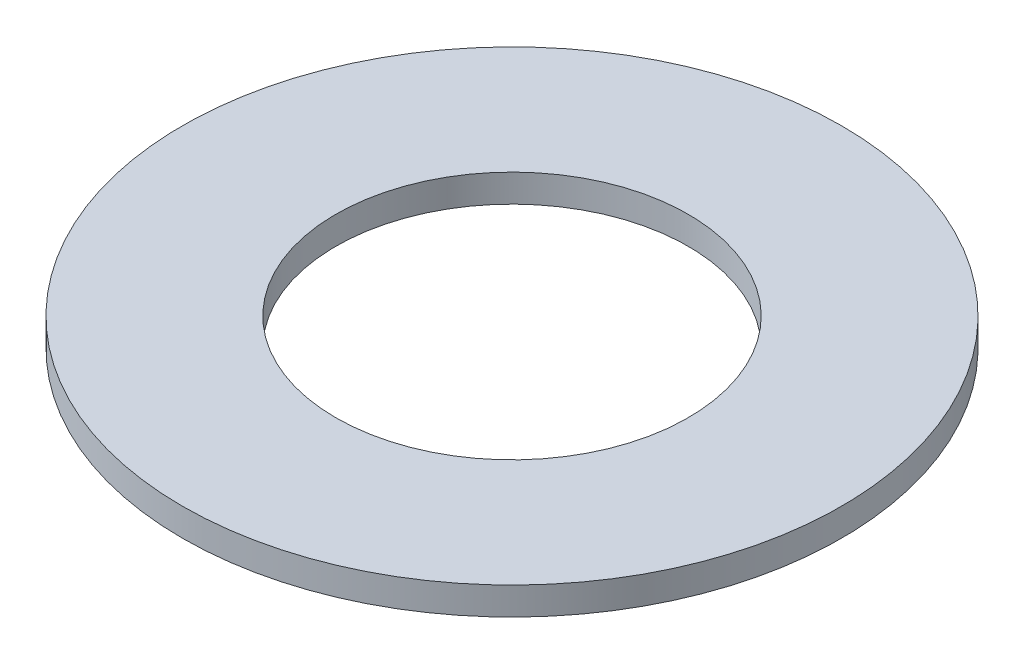
SolidWorks part; units mm, degrees
material "6061-T4 (SS)"
ref_plane "Front Plane" through (0, 0, 0) normal (0, 0, 1) x (1, 0, 0)
ref_plane "Top Plane" through (0, 0, 0) normal (0, 1, 0) x (1, 0, 0)
ref_plane "Right Plane" through (0, 0, 0) normal (1, 0, 0) x (0, 0, -1)
sketch "Sketch1" plane through (0, 0, 0) normal (0, 1, 0) x (1, 0, 0)
  circle A0 centre (0, 0) radius 4.75
  dimension "D1" = 9.5
extrude "Boss-Extrude1" add sketch "Sketch1" along normal blind 0.4
sketch "Sketch2" plane through (0, 0.4, 0) normal (0, 1, 0) x (1, 0, 0)
  circle A0 centre (0, 0) radius 2.54
  dimension "D1" = 5.08
extrude "Cut-Extrude1" cut sketch "Sketch2" against normal blind 0.4
